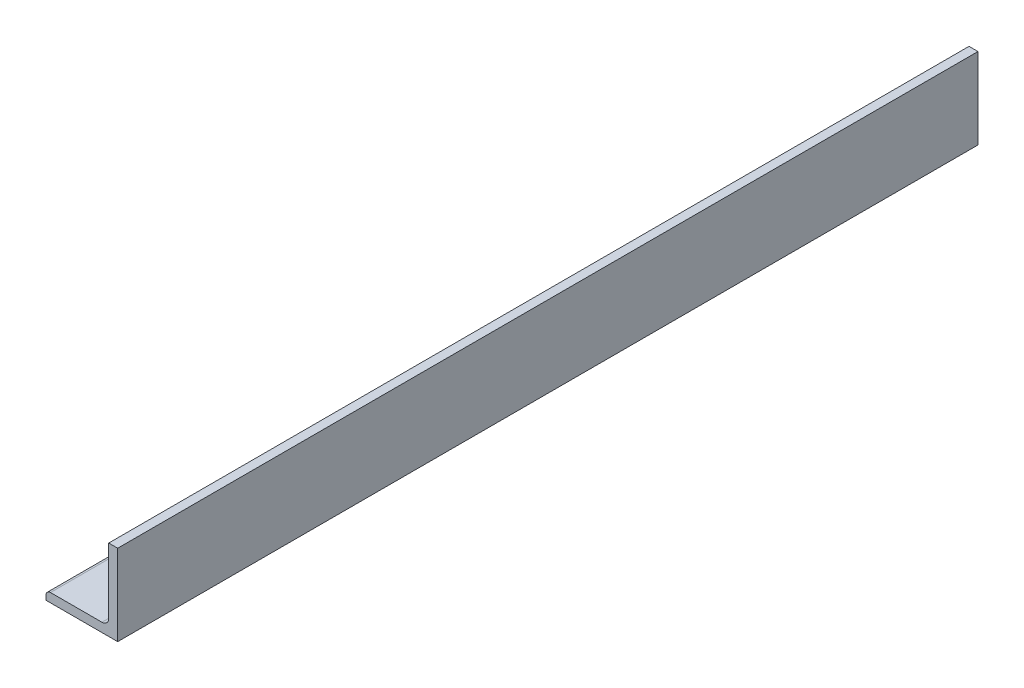
SolidWorks part; units mm, degrees
material "6061-T6 (SS)"
ref_plane "Front Plane" through (0, 0, 0) normal (0, 0, 1) x (1, 0, 0)
ref_plane "Top Plane" through (0, 0, 0) normal (0, 1, 0) x (1, 0, 0)
ref_plane "Right Plane" through (0, 0, 0) normal (1, 0, 0) x (0, 0, -1)
sketch "Sketch0" plane through (0, 0, 0) normal (0, 0, 1) x (1, 0, 0)
  line L0 (-25.4, -38.1) -> (25.4, -38.1)
  line L1 (25.4, -38.1) -> (25.4, 38.1)
  line L2 (25.4, 0) -> (0, 0) construction
  line L3 (0, 0) -> (0, -38.1) construction
  line L4 (19.05, -26.9748) -> (19.05, 38.1) construction
  line L5 (14.2748, -31.75) -> (-25.4, -31.75) construction
  arc A0 (19.05, -26.9748) -> (14.2748, -31.75) centre (14.2748, -26.9748) cw
  point P3 (17.6514, -30.3514)
  dimension "Inside Corner Radius" = 4.7752
  dimension "Outside Height" = 76.2
  dimension "Inside Height" = 69.85
  dimension "Inside Width" = 44.45
  dimension "Wall Thickness" = 6.35
  dimension "D1" = 6.35
  dimension "Outside Width" = 50.8
sketch "Sketch1" plane through (0, 0, 0) normal (1, 0, 0) x (0, 0, -1)
  line L0 (304.8, 0) -> (-304.8, 0)
  point P4 (0, 0)
  dimension "Length" = 609.6
sketch "Sketch2" plane through (0, 0, 0) normal (0, 0, 1) x (1, 0, 0)
  line L0 (-25.4, -38.1) -> (25.4, -38.1)
  line L1 (25.4, -38.1) -> (25.4, 38.1)
  line L2 (25.4, 38.1) -> (19.05, 38.1) construction
  line L3 (19.05, 34.925) -> (19.05, -26.9748)
  line L4 (14.2748, -31.75) -> (-22.225, -31.75)
  line L5 (-25.4, -38.1) -> (-25.4, -31.75) construction
  line L6 (22.225, 38.1) -> (25.4, 38.1)
  line L7 (-25.4, -34.925) -> (-25.4, -38.1)
  line L8 (25.4, 0) -> (0, 0) construction
  line L9 (0, 0) -> (0, -38.1) construction
  arc A0 (19.05, 34.925) -> (22.225, 38.1) centre (22.225, 34.925) cw
  arc A1 (-25.4, -34.925) -> (-22.225, -31.75) centre (-22.225, -34.925) cw
  arc A2 (19.05, -26.9748) -> (14.2748, -31.75) centre (14.2748, -26.9748) cw
  dimension "Inside Radius" = 4.7752
  dimension "Height" = 76.2
  dimension "Width" = 50.8
  dimension "Thickness" = 6.35
extrude "Boss-Extrude1" add sketch "Sketch2" along normal mid plane 609.6
sketch "Break Locations" plane through (0, 0, 0) normal (1, 0, 0) x (0, 0, -1)
  line L0 (-227.076, 0) -> (227.076, 0)
  line L1 (-304.8, -38.1) -> (-304.8, 38.1) construction
  line L2 (304.8, -38.1) -> (304.8, 38.1) construction
  point P0 (-240.03, 0)
  point P1 (240.03, 0)
  point P10 (0, 0)
  point P11 (227.076, 0)
  point P13 (-227.076, 0)
  dimension "D1" = 64.77
  dimension "D2" = 64.77
  dimension "D3" = 77.724
sketch "Sketch3" plane through (0, 0, 304.8) normal (0, 0, 1) x (1, 0, 0)
  line L1 (8.7689, 40.8576) -> (38.7898, 40.8576)
  line L2 (8.7689, 40.8576) -> (8.7689, 19.2609)
  line L3 (8.7689, 19.2609) -> (38.7898, 19.2609)
  line L4 (38.7898, 40.8576) -> (38.7898, 19.2609)
extrude "Cut-Extrude1" cut sketch "Sketch3" against normal through all
equation "\"D1@Break Locations\" = .85 * \"Height@Sketch2\""
equation "\"D2@Break Locations\"=\"D1@Break Locations\""
equation "\"Thickness@Sketch2\" = \"Wall Thickness@Sketch0\""
equation "\"Height@Sketch2\" = \"Outside Height@Sketch0\""
equation "\"Width@Sketch2\" = \"Outside Width@Sketch0\""
equation "\"Inside Radius@Sketch2\" = \"Inside Corner Radius@Sketch0\""
equation "\"Length@Boss-Extrude1\" = \"Length@Sketch1\""
equation "\"D3@Break Locations\"=\"D2@Break Locations\"*1.2"
equation "\"D1@Sketch0\"=\"Wall Thickness@Sketch0\""
